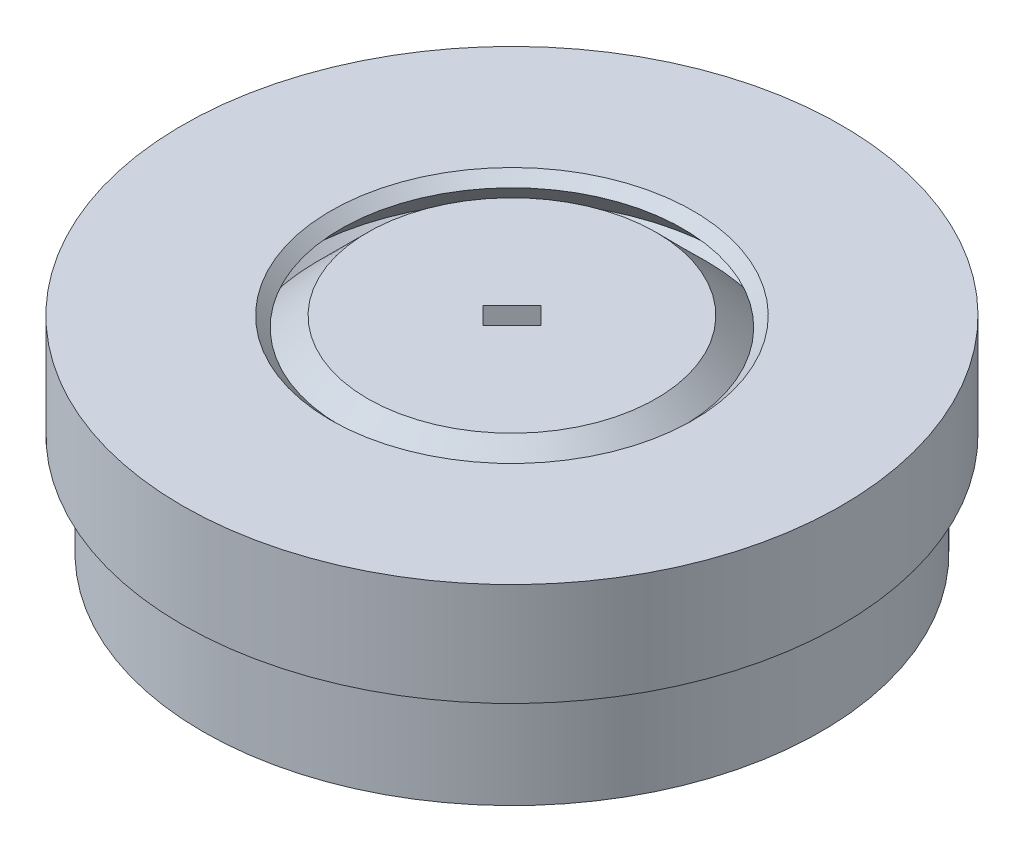
SolidWorks part; units mm, degrees
ref_plane "Front Plane" through (0, 0, 0) normal (0, 0, 1) x (1, 0, 0)
ref_plane "Top Plane" through (0, 0, 0) normal (0, 1, 0) x (1, 0, 0)
ref_plane "Right Plane" through (0, 0, 0) normal (1, 0, 0) x (0, 0, -1)
sketch "Sketch3" plane through (0, 0, 0) normal (0, 1, 0) x (1, 0, 0)
  line L0 (0, 0) -> (0, 14) construction
  line L1 (0, 11) -> (0, 14)
  line L2 (6.4656, 8.8992) -> (8.229, 11.3262)
  line L3 (10.4616, 3.3992) -> (13.3148, 4.3262)
  line L4 (10.4616, -3.3992) -> (13.3148, -4.3262)
  line L5 (6.4656, -8.8992) -> (8.229, -11.3262)
  line L6 (0, -11) -> (0, -14)
  line L7 (-6.4656, -8.8992) -> (-8.229, -11.3262)
  line L8 (-10.4616, -3.3992) -> (-13.3148, -4.3262)
  line L9 (-10.4616, 3.3992) -> (-13.3148, 4.3262)
  line L10 (-6.4656, 8.8992) -> (-8.229, 11.3262)
  line L12 (3, 3) -> (-3, 3)
  line L13 (3, 3) -> (3, -3)
  line L14 (3, -3) -> (-3, -3)
  line L15 (-3, 3) -> (-3, -3)
  line L16 (0, -3) -> (0, 3) construction
  line L17 (3, 0) -> (-3, 0) construction
  circle A0 centre (0, 0) radius 15
  circle A1 centre (0, 0) radius 14 construction
  spline S0 degree 4 poles (-0.6778, 10.6763) (-0.6286, 10.7014) (-0.5336, 10.7495) (-0.4182, 10.8106) (-0.084, 10.9641) (0.0577, 11.0264) (0.4379, 11.1818) (0.6637, 11.2619) (0.971, 11.3685) (1.234, 11.4472) (1.5272, 11.5305) (1.8056, 11.5989) (2.0959, 11.6642) (2.3817, 11.7192) (2.6725, 11.7684) (2.9623, 11.8092) (3.2542, 11.8431) (3.5945, 11.8737) (4.009, 11.8986) (4.4979, 11.9088) (4.9859, 11.897) (5.4262, 11.8684) (5.7898, 11.8338) (6.0839, 11.7981) (6.4416, 11.7478) (6.8131, 11.6815) (7.1561, 11.6125) (7.5364, 11.5205) (7.7792, 11.459) (8.1801, 11.3427) (8.3369, 11.2932) (8.7269, 11.165) (8.8594, 11.1137) (8.9726, 11.0725) (9.0307, 11.0511) knots 0 0 0 0 0 0.018755 0.037509 0.074516 0.103872 0.133229 0.162585 0.191942 0.221299 0.250655 0.280012 0.309368 0.338725 0.368082 0.397438 0.426795 0.456151 0.504872 0.563586 0.622299 0.651656 0.681012 0.710369 0.739725 0.798439 0.827795 0.857152 0.886508 0.915865 0.957933 0.978966 1 1 1 1 1 construction
  spline S1 degree 4 poles (0, 11) (0.0566, 11.0246) (0.1702, 11.0724) (0.4379, 11.1818) (0.6637, 11.2619) (0.971, 11.3685) (1.234, 11.4472) (1.5272, 11.5305) (1.8056, 11.5989) (2.0959, 11.6642) (2.3817, 11.7192) (2.6725, 11.7684) (2.9623, 11.8092) (3.2542, 11.8431) (3.5945, 11.8737) (4.009, 11.8986) (4.4979, 11.9088) (4.9859, 11.897) (5.4262, 11.8684) (5.7898, 11.8338) (6.0839, 11.7981) (6.4416, 11.7478) (6.8131, 11.6815) (7.1561, 11.6125) (7.5364, 11.5205) (7.7792, 11.459) (8.0505, 11.3803) (8.17, 11.3445) (8.229, 11.3262) knots 0.074516 0.074516 0.074516 0.074516 0.074516 0.103872 0.133229 0.162585 0.191942 0.221299 0.250655 0.280012 0.309368 0.338725 0.368082 0.397438 0.426795 0.456151 0.504872 0.563586 0.622299 0.651656 0.681012 0.710369 0.739725 0.798439 0.827795 0.857152 0.886508 0.915865 0.915865 0.915865 0.915865 0.915865
  spline S2 degree 4 poles (5.727, 9.0357) (5.7816, 9.0271) (5.8867, 9.0101) (6.016, 8.9918) (6.3766, 8.9195) (6.5279, 8.8866) (6.9268, 8.7889) (7.1565, 8.7209) (7.4678, 8.6266) (7.7268, 8.5357) (8.013, 8.4307) (8.2785, 8.3224) (8.5517, 8.2045) (8.8152, 8.0811) (9.0794, 7.95) (9.3378, 7.8126) (9.5939, 7.6685) (9.8872, 7.4932) (10.2371, 7.2697) (10.6387, 6.9906) (11.0265, 6.6943) (11.3659, 6.4123) (11.6398, 6.1706) (11.8567, 5.9689) (12.1165, 5.7179) (12.3781, 5.4459) (12.6151, 5.1885) (12.8687, 4.8905) (13.029, 4.698) (13.2848, 4.3683) (13.3827, 4.236) (13.6228, 3.9031) (13.6999, 3.7838) (13.7672, 3.6839) (13.8017, 3.6324) knots 0 0 0 0 0 0.018755 0.037509 0.074516 0.103872 0.133229 0.162585 0.191942 0.221299 0.250655 0.280012 0.309368 0.338725 0.368082 0.397438 0.426795 0.456151 0.504872 0.563586 0.622299 0.651656 0.681012 0.710369 0.739725 0.798439 0.827795 0.857152 0.886508 0.915865 0.957933 0.978966 1 1 1 1 1 construction
  spline S3 degree 4 poles (6.4656, 8.8992) (6.5259, 8.8858) (6.6459, 8.8577) (6.9268, 8.7889) (7.1565, 8.7209) (7.4678, 8.6266) (7.7268, 8.5357) (8.013, 8.4307) (8.2785, 8.3224) (8.5517, 8.2045) (8.8152, 8.0811) (9.0794, 7.95) (9.3378, 7.8126) (9.5939, 7.6685) (9.8872, 7.4932) (10.2371, 7.2697) (10.6387, 6.9906) (11.0265, 6.6943) (11.3659, 6.4123) (11.6398, 6.1706) (11.8567, 5.9689) (12.1165, 5.7179) (12.3781, 5.4459) (12.6151, 5.1885) (12.8687, 4.8905) (13.029, 4.698) (13.2021, 4.4749) (13.2778, 4.3756) (13.3148, 4.3262) knots 0.074516 0.074516 0.074516 0.074516 0.074516 0.103872 0.133229 0.162585 0.191942 0.221299 0.250655 0.280012 0.309368 0.338725 0.368082 0.397438 0.426795 0.456151 0.504872 0.563586 0.622299 0.651656 0.681012 0.710369 0.739725 0.798439 0.827795 0.857152 0.886508 0.915865 0.915865 0.915865 0.915865 0.915865
  spline S4 degree 4 poles (9.9443, 3.9438) (9.9834, 3.9047) (10.0585, 3.8292) (10.1522, 3.7384) (10.4015, 3.468) (10.5046, 3.3524) (10.7698, 3.0389) (10.9158, 2.8489) (11.1122, 2.5895) (11.2683, 2.3638) (11.4381, 2.1106) (11.5892, 1.867) (11.7409, 1.6111) (11.8816, 1.3563) (12.0183, 1.095) (12.1466, 0.8319) (12.2691, 0.5648) (12.4033, 0.2506) (12.5551, -0.1359) (12.7158, -0.5977) (12.8555, -1.0654) (12.9643, -1.493) (13.0438, -1.8496) (13.1007, -2.1403) (13.1634, -2.496) (13.2151, -2.8698) (13.2555, -3.2174) (13.2855, -3.6076) (13.3021, -3.8575) (13.3153, -4.2746) (13.3167, -4.4391) (13.3153, -4.8496) (13.3075, -4.9915) (13.3032, -5.1118) (13.3009, -5.1737) knots 0 0 0 0 0 0.018755 0.037509 0.074516 0.103872 0.133229 0.162585 0.191942 0.221299 0.250655 0.280012 0.309368 0.338725 0.368082 0.397438 0.426795 0.456151 0.504872 0.563586 0.622299 0.651656 0.681012 0.710369 0.739725 0.798439 0.827795 0.857152 0.886508 0.915865 0.957933 0.978966 1 1 1 1 1 construction
  spline S5 degree 4 poles (10.4616, 3.3992) (10.5025, 3.3529) (10.583, 3.2597) (10.7698, 3.0389) (10.9158, 2.8489) (11.1122, 2.5895) (11.2683, 2.3638) (11.4381, 2.1106) (11.5892, 1.867) (11.7409, 1.6111) (11.8816, 1.3563) (12.0183, 1.095) (12.1466, 0.8319) (12.2691, 0.5648) (12.4033, 0.2506) (12.5551, -0.1359) (12.7158, -0.5977) (12.8555, -1.0654) (12.9643, -1.493) (13.0438, -1.8496) (13.1007, -2.1403) (13.1634, -2.496) (13.2151, -2.8698) (13.2555, -3.2174) (13.2855, -3.6076) (13.3021, -3.8575) (13.311, -4.1398) (13.3139, -4.2645) (13.3148, -4.3262) knots 0.074516 0.074516 0.074516 0.074516 0.074516 0.103872 0.133229 0.162585 0.191942 0.221299 0.250655 0.280012 0.309368 0.338725 0.368082 0.397438 0.426795 0.456151 0.504872 0.563586 0.622299 0.651656 0.681012 0.710369 0.739725 0.798439 0.827795 0.857152 0.886508 0.915865 0.915865 0.915865 0.915865 0.915865
  spline S6 degree 4 poles (10.3632, -2.6545) (10.3719, -2.7091) (10.3882, -2.8143) (10.4107, -2.9429) (10.4535, -3.3082) (10.4689, -3.4622) (10.4992, -3.8718) (10.5056, -4.1113) (10.512, -4.4366) (10.5056, -4.711) (10.4942, -5.0156) (10.4732, -5.3015) (10.4456, -5.5978) (10.4097, -5.8866) (10.3666, -6.1783) (10.3158, -6.4665) (10.2579, -6.7546) (10.1818, -7.0878) (10.0774, -7.4896) (9.936, -7.9578) (9.774, -8.4182) (9.6108, -8.8281) (9.4655, -9.1633) (9.3407, -9.4319) (9.1823, -9.7566) (9.0044, -10.0894) (8.8328, -10.3943) (8.6277, -10.7276) (8.4943, -10.9395) (8.2597, -11.2848) (8.1642, -11.4187) (7.9218, -11.7499) (7.8321, -11.8601) (7.7579, -11.955) (7.7196, -12.0037) knots 0 0 0 0 0 0.018755 0.037509 0.074516 0.103872 0.133229 0.162585 0.191942 0.221299 0.250655 0.280012 0.309368 0.338725 0.368082 0.397438 0.426795 0.456151 0.504872 0.563586 0.622299 0.651656 0.681012 0.710369 0.739725 0.798439 0.827795 0.857152 0.886508 0.915865 0.957933 0.978966 1 1 1 1 1 construction
  spline S7 degree 4 poles (10.4616, -3.3992) (10.4675, -3.4606) (10.4779, -3.5834) (10.4992, -3.8718) (10.5056, -4.1113) (10.512, -4.4366) (10.5056, -4.711) (10.4942, -5.0156) (10.4732, -5.3015) (10.4456, -5.5978) (10.4097, -5.8866) (10.3666, -6.1783) (10.3158, -6.4665) (10.2579, -6.7546) (10.1818, -7.0878) (10.0774, -7.4896) (9.936, -7.9578) (9.774, -8.4182) (9.6108, -8.8281) (9.4655, -9.1633) (9.3407, -9.4319) (9.1823, -9.7566) (9.0044, -10.0894) (8.8328, -10.3943) (8.6277, -10.7276) (8.4943, -10.9395) (8.3355, -11.1732) (8.2645, -11.2758) (8.229, -11.3262) knots 0.074516 0.074516 0.074516 0.074516 0.074516 0.103872 0.133229 0.162585 0.191942 0.221299 0.250655 0.280012 0.309368 0.338725 0.368082 0.397438 0.426795 0.456151 0.504872 0.563586 0.622299 0.651656 0.681012 0.710369 0.739725 0.798439 0.827795 0.857152 0.886508 0.915865 0.915865 0.915865 0.915865 0.915865
  spline S8 degree 4 poles (6.8238, -8.2389) (6.7987, -8.2881) (6.75, -8.3829) (6.6926, -8.5001) (6.5125, -8.8208) (6.4344, -8.9545) (6.2182, -9.3037) (6.0826, -9.5012) (5.8967, -9.7681) (5.7302, -9.9863) (5.5419, -10.2261) (5.3569, -10.445) (5.1604, -10.6685) (4.9615, -10.881) (4.7552, -11.0917) (4.5447, -11.295) (4.3285, -11.4941) (4.0712, -11.7188) (3.7505, -11.9826) (3.3609, -12.2782) (2.9593, -12.5555) (2.5862, -12.7912) (2.2717, -12.9769) (2.0128, -13.1209) (1.6938, -13.2904) (1.3544, -13.4552) (1.0362, -13.601) (0.6745, -13.7501) (0.4419, -13.8431) (0.0492, -13.9845) (-0.1068, -14.0367) (-0.4976, -14.1622) (-0.6349, -14.1986) (-0.7507, -14.2318) (-0.8103, -14.2487) knots 0 0 0 0 0 0.018755 0.037509 0.074516 0.103872 0.133229 0.162585 0.191942 0.221299 0.250655 0.280012 0.309368 0.338725 0.368082 0.397438 0.426795 0.456151 0.504872 0.563586 0.622299 0.651656 0.681012 0.710369 0.739725 0.798439 0.827795 0.857152 0.886508 0.915865 0.957933 0.978966 1 1 1 1 1 construction
  spline S9 degree 4 poles (6.4656, -8.8992) (6.4343, -8.9523) (6.3705, -9.0578) (6.2182, -9.3037) (6.0826, -9.5012) (5.8967, -9.7681) (5.7302, -9.9863) (5.5419, -10.2261) (5.3569, -10.445) (5.1604, -10.6685) (4.9615, -10.881) (4.7552, -11.0917) (4.5447, -11.295) (4.3285, -11.4941) (4.0712, -11.7188) (3.7505, -11.9826) (3.3609, -12.2782) (2.9593, -12.5555) (2.5862, -12.7912) (2.2717, -12.9769) (2.0128, -13.1209) (1.6938, -13.2904) (1.3544, -13.4552) (1.0362, -13.601) (0.6745, -13.7501) (0.4419, -13.8431) (0.1762, -13.9388) (0.0584, -13.9801) (0, -14) knots 0.074516 0.074516 0.074516 0.074516 0.074516 0.103872 0.133229 0.162585 0.191942 0.221299 0.250655 0.280012 0.309368 0.338725 0.368082 0.397438 0.426795 0.456151 0.504872 0.563586 0.622299 0.651656 0.681012 0.710369 0.739725 0.798439 0.827795 0.857152 0.886508 0.915865 0.915865 0.915865 0.915865 0.915865
  spline S10 degree 4 poles (0.6778, -10.6763) (0.6286, -10.7014) (0.5336, -10.7495) (0.4182, -10.8106) (0.084, -10.9641) (-0.0577, -11.0264) (-0.4379, -11.1818) (-0.6637, -11.2619) (-0.971, -11.3685) (-1.234, -11.4472) (-1.5272, -11.5305) (-1.8056, -11.5989) (-2.0959, -11.6642) (-2.3817, -11.7192) (-2.6725, -11.7684) (-2.9623, -11.8092) (-3.2542, -11.8431) (-3.5945, -11.8737) (-4.009, -11.8986) (-4.4979, -11.9088) (-4.9859, -11.897) (-5.4262, -11.8684) (-5.7898, -11.8338) (-6.0839, -11.7981) (-6.4416, -11.7478) (-6.8131, -11.6815) (-7.1561, -11.6125) (-7.5364, -11.5205) (-7.7792, -11.459) (-8.1801, -11.3427) (-8.3369, -11.2932) (-8.7269, -11.165) (-8.8594, -11.1137) (-8.9726, -11.0725) (-9.0307, -11.0511) knots 0 0 0 0 0 0.018755 0.037509 0.074516 0.103872 0.133229 0.162585 0.191942 0.221299 0.250655 0.280012 0.309368 0.338725 0.368082 0.397438 0.426795 0.456151 0.504872 0.563586 0.622299 0.651656 0.681012 0.710369 0.739725 0.798439 0.827795 0.857152 0.886508 0.915865 0.957933 0.978966 1 1 1 1 1 construction
  spline S11 degree 4 poles (0, -11) (-0.0566, -11.0246) (-0.1702, -11.0724) (-0.4379, -11.1818) (-0.6637, -11.2619) (-0.971, -11.3685) (-1.234, -11.4472) (-1.5272, -11.5305) (-1.8056, -11.5989) (-2.0959, -11.6642) (-2.3817, -11.7192) (-2.6725, -11.7684) (-2.9623, -11.8092) (-3.2542, -11.8431) (-3.5945, -11.8737) (-4.009, -11.8986) (-4.4979, -11.9088) (-4.9859, -11.897) (-5.4262, -11.8684) (-5.7898, -11.8338) (-6.0839, -11.7981) (-6.4416, -11.7478) (-6.8131, -11.6815) (-7.1561, -11.6125) (-7.5364, -11.5205) (-7.7792, -11.459) (-8.0505, -11.3803) (-8.17, -11.3445) (-8.229, -11.3262) knots 0.074516 0.074516 0.074516 0.074516 0.074516 0.103872 0.133229 0.162585 0.191942 0.221299 0.250655 0.280012 0.309368 0.338725 0.368082 0.397438 0.426795 0.456151 0.504872 0.563586 0.622299 0.651656 0.681012 0.710369 0.739725 0.798439 0.827795 0.857152 0.886508 0.915865 0.915865 0.915865 0.915865 0.915865
  spline S12 degree 4 poles (-5.727, -9.0357) (-5.7816, -9.0271) (-5.8867, -9.0101) (-6.016, -8.9918) (-6.3766, -8.9195) (-6.5279, -8.8866) (-6.9268, -8.7889) (-7.1565, -8.7209) (-7.4678, -8.6266) (-7.7268, -8.5357) (-8.013, -8.4307) (-8.2785, -8.3224) (-8.5517, -8.2045) (-8.8152, -8.0811) (-9.0794, -7.95) (-9.3378, -7.8126) (-9.5939, -7.6685) (-9.8872, -7.4932) (-10.2371, -7.2697) (-10.6387, -6.9906) (-11.0265, -6.6943) (-11.3659, -6.4123) (-11.6398, -6.1706) (-11.8567, -5.9689) (-12.1165, -5.7179) (-12.3781, -5.4459) (-12.6151, -5.1885) (-12.8687, -4.8905) (-13.029, -4.698) (-13.2848, -4.3683) (-13.3827, -4.236) (-13.6228, -3.9031) (-13.6999, -3.7838) (-13.7672, -3.6839) (-13.8017, -3.6324) knots 0 0 0 0 0 0.018755 0.037509 0.074516 0.103872 0.133229 0.162585 0.191942 0.221299 0.250655 0.280012 0.309368 0.338725 0.368082 0.397438 0.426795 0.456151 0.504872 0.563586 0.622299 0.651656 0.681012 0.710369 0.739725 0.798439 0.827795 0.857152 0.886508 0.915865 0.957933 0.978966 1 1 1 1 1 construction
  spline S13 degree 4 poles (-6.4656, -8.8992) (-6.5259, -8.8858) (-6.6459, -8.8577) (-6.9268, -8.7889) (-7.1565, -8.7209) (-7.4678, -8.6266) (-7.7268, -8.5357) (-8.013, -8.4307) (-8.2785, -8.3224) (-8.5517, -8.2045) (-8.8152, -8.0811) (-9.0794, -7.95) (-9.3378, -7.8126) (-9.5939, -7.6685) (-9.8872, -7.4932) (-10.2371, -7.2697) (-10.6387, -6.9906) (-11.0265, -6.6943) (-11.3659, -6.4123) (-11.6398, -6.1706) (-11.8567, -5.9689) (-12.1165, -5.7179) (-12.3781, -5.4459) (-12.6151, -5.1885) (-12.8687, -4.8905) (-13.029, -4.698) (-13.2021, -4.4749) (-13.2778, -4.3756) (-13.3148, -4.3262) knots 0.074516 0.074516 0.074516 0.074516 0.074516 0.103872 0.133229 0.162585 0.191942 0.221299 0.250655 0.280012 0.309368 0.338725 0.368082 0.397438 0.426795 0.456151 0.504872 0.563586 0.622299 0.651656 0.681012 0.710369 0.739725 0.798439 0.827795 0.857152 0.886508 0.915865 0.915865 0.915865 0.915865 0.915865
  spline S14 degree 4 poles (-9.9443, -3.9438) (-9.9834, -3.9047) (-10.0585, -3.8292) (-10.1522, -3.7384) (-10.4015, -3.468) (-10.5046, -3.3524) (-10.7698, -3.0389) (-10.9158, -2.8489) (-11.1122, -2.5895) (-11.2683, -2.3638) (-11.4381, -2.1106) (-11.5892, -1.867) (-11.7409, -1.6111) (-11.8816, -1.3563) (-12.0183, -1.095) (-12.1466, -0.8319) (-12.2691, -0.5648) (-12.4033, -0.2506) (-12.5551, 0.1359) (-12.7158, 0.5977) (-12.8555, 1.0654) (-12.9643, 1.493) (-13.0438, 1.8496) (-13.1007, 2.1403) (-13.1634, 2.496) (-13.2151, 2.8698) (-13.2555, 3.2174) (-13.2855, 3.6076) (-13.3021, 3.8575) (-13.3153, 4.2746) (-13.3167, 4.4391) (-13.3153, 4.8496) (-13.3075, 4.9915) (-13.3032, 5.1118) (-13.3009, 5.1737) knots 0 0 0 0 0 0.018755 0.037509 0.074516 0.103872 0.133229 0.162585 0.191942 0.221299 0.250655 0.280012 0.309368 0.338725 0.368082 0.397438 0.426795 0.456151 0.504872 0.563586 0.622299 0.651656 0.681012 0.710369 0.739725 0.798439 0.827795 0.857152 0.886508 0.915865 0.957933 0.978966 1 1 1 1 1 construction
  spline S15 degree 4 poles (-10.4616, -3.3992) (-10.5025, -3.3529) (-10.583, -3.2597) (-10.7698, -3.0389) (-10.9158, -2.8489) (-11.1122, -2.5895) (-11.2683, -2.3638) (-11.4381, -2.1106) (-11.5892, -1.867) (-11.7409, -1.6111) (-11.8816, -1.3563) (-12.0183, -1.095) (-12.1466, -0.8319) (-12.2691, -0.5648) (-12.4033, -0.2506) (-12.5551, 0.1359) (-12.7158, 0.5977) (-12.8555, 1.0654) (-12.9643, 1.493) (-13.0438, 1.8496) (-13.1007, 2.1403) (-13.1634, 2.496) (-13.2151, 2.8698) (-13.2555, 3.2174) (-13.2855, 3.6076) (-13.3021, 3.8575) (-13.311, 4.1398) (-13.3139, 4.2645) (-13.3148, 4.3262) knots 0.074516 0.074516 0.074516 0.074516 0.074516 0.103872 0.133229 0.162585 0.191942 0.221299 0.250655 0.280012 0.309368 0.338725 0.368082 0.397438 0.426795 0.456151 0.504872 0.563586 0.622299 0.651656 0.681012 0.710369 0.739725 0.798439 0.827795 0.857152 0.886508 0.915865 0.915865 0.915865 0.915865 0.915865
  spline S16 degree 4 poles (-10.3632, 2.6545) (-10.3719, 2.7091) (-10.3882, 2.8143) (-10.4107, 2.9429) (-10.4535, 3.3082) (-10.4689, 3.4622) (-10.4992, 3.8718) (-10.5056, 4.1113) (-10.512, 4.4366) (-10.5056, 4.711) (-10.4942, 5.0156) (-10.4732, 5.3015) (-10.4456, 5.5978) (-10.4097, 5.8866) (-10.3666, 6.1783) (-10.3158, 6.4665) (-10.2579, 6.7546) (-10.1818, 7.0878) (-10.0774, 7.4896) (-9.936, 7.9578) (-9.774, 8.4182) (-9.6108, 8.8281) (-9.4655, 9.1633) (-9.3407, 9.4319) (-9.1823, 9.7566) (-9.0044, 10.0894) (-8.8328, 10.3943) (-8.6277, 10.7276) (-8.4943, 10.9395) (-8.2597, 11.2848) (-8.1642, 11.4187) (-7.9218, 11.7499) (-7.8321, 11.8601) (-7.7579, 11.955) (-7.7196, 12.0037) knots 0 0 0 0 0 0.018755 0.037509 0.074516 0.103872 0.133229 0.162585 0.191942 0.221299 0.250655 0.280012 0.309368 0.338725 0.368082 0.397438 0.426795 0.456151 0.504872 0.563586 0.622299 0.651656 0.681012 0.710369 0.739725 0.798439 0.827795 0.857152 0.886508 0.915865 0.957933 0.978966 1 1 1 1 1 construction
  spline S17 degree 4 poles (-10.4616, 3.3992) (-10.4675, 3.4606) (-10.4779, 3.5834) (-10.4992, 3.8718) (-10.5056, 4.1113) (-10.512, 4.4366) (-10.5056, 4.711) (-10.4942, 5.0156) (-10.4732, 5.3015) (-10.4456, 5.5978) (-10.4097, 5.8866) (-10.3666, 6.1783) (-10.3158, 6.4665) (-10.2579, 6.7546) (-10.1818, 7.0878) (-10.0774, 7.4896) (-9.936, 7.9578) (-9.774, 8.4182) (-9.6108, 8.8281) (-9.4655, 9.1633) (-9.3407, 9.4319) (-9.1823, 9.7566) (-9.0044, 10.0894) (-8.8328, 10.3943) (-8.6277, 10.7276) (-8.4943, 10.9395) (-8.3355, 11.1732) (-8.2645, 11.2758) (-8.229, 11.3262) knots 0.074516 0.074516 0.074516 0.074516 0.074516 0.103872 0.133229 0.162585 0.191942 0.221299 0.250655 0.280012 0.309368 0.338725 0.368082 0.397438 0.426795 0.456151 0.504872 0.563586 0.622299 0.651656 0.681012 0.710369 0.739725 0.798439 0.827795 0.857152 0.886508 0.915865 0.915865 0.915865 0.915865 0.915865
  spline S18 degree 4 poles (-6.8238, 8.2389) (-6.7987, 8.2881) (-6.75, 8.3829) (-6.6926, 8.5001) (-6.5125, 8.8208) (-6.4344, 8.9545) (-6.2182, 9.3037) (-6.0826, 9.5012) (-5.8967, 9.7681) (-5.7302, 9.9863) (-5.5419, 10.2261) (-5.3569, 10.445) (-5.1604, 10.6685) (-4.9615, 10.881) (-4.7552, 11.0917) (-4.5447, 11.295) (-4.3285, 11.4941) (-4.0712, 11.7188) (-3.7505, 11.9826) (-3.3609, 12.2782) (-2.9593, 12.5555) (-2.5862, 12.7912) (-2.2717, 12.9769) (-2.0128, 13.1209) (-1.6938, 13.2904) (-1.3544, 13.4552) (-1.0362, 13.601) (-0.6745, 13.7501) (-0.4419, 13.8431) (-0.0492, 13.9845) (0.1068, 14.0367) (0.4976, 14.1622) (0.6349, 14.1986) (0.7507, 14.2318) (0.8103, 14.2487) knots 0 0 0 0 0 0.018755 0.037509 0.074516 0.103872 0.133229 0.162585 0.191942 0.221299 0.250655 0.280012 0.309368 0.338725 0.368082 0.397438 0.426795 0.456151 0.504872 0.563586 0.622299 0.651656 0.681012 0.710369 0.739725 0.798439 0.827795 0.857152 0.886508 0.915865 0.957933 0.978966 1 1 1 1 1 construction
  spline S19 degree 4 poles (-6.4656, 8.8992) (-6.4343, 8.9523) (-6.3705, 9.0578) (-6.2182, 9.3037) (-6.0826, 9.5012) (-5.8967, 9.7681) (-5.7302, 9.9863) (-5.5419, 10.2261) (-5.3569, 10.445) (-5.1604, 10.6685) (-4.9615, 10.881) (-4.7552, 11.0917) (-4.5447, 11.295) (-4.3285, 11.4941) (-4.0712, 11.7188) (-3.7505, 11.9826) (-3.3609, 12.2782) (-2.9593, 12.5555) (-2.5862, 12.7912) (-2.2717, 12.9769) (-2.0128, 13.1209) (-1.6938, 13.2904) (-1.3544, 13.4552) (-1.0362, 13.601) (-0.6745, 13.7501) (-0.4419, 13.8431) (-0.1762, 13.9388) (-0.0584, 13.9801) (0, 14) knots 0.074516 0.074516 0.074516 0.074516 0.074516 0.103872 0.133229 0.162585 0.191942 0.221299 0.250655 0.280012 0.309368 0.338725 0.368082 0.397438 0.426795 0.456151 0.504872 0.563586 0.622299 0.651656 0.681012 0.710369 0.739725 0.798439 0.827795 0.857152 0.886508 0.915865 0.915865 0.915865 0.915865 0.915865
  point P57 (0, 0)
  dimension "D1" = 30
  dimension "D2" = 28
  dimension "D3" = 10
  dimension "D4" = 6
  dimension "D5" = 6
extrude "Boss-Extrude1" add sketch "Sketch3" along normal blind 3 contours A0 L10 S19 L1 S1 L2 S3 L3 S5 L4 S7 L5 S9 L6 S11 L7 S13 L8 S15 L9 S17 | L13 L12 L15 L14
sketch "Sketch5" plane through (0, 0, 0) normal (1, 0, 0) x (0, 0, -1)
  line L0 (-3, 0) -> (-3, 3) construction
  line L1 (-3, 3) -> (3, 3) construction
  line L2 (3, 3) -> (3, 0) construction
  line L3 (3, 0) -> (-3, 0) construction
  line L4 (-3, 3) -> (3, 0) construction
  line L5 (-3, 0) -> (3, 3) construction
  line L6 (15, 0) -> (15, 3) construction
  line L7 (-15, 3) -> (15, 3) construction
  line L8 (-15, 3) -> (-15, 10) construction
  line L9 (-15, 10) -> (15, 10) construction
  line L10 (15, 3) -> (15, 10) construction
  line L11 (0, 10) -> (0, 3) construction
  line L12 (-15, 6.5) -> (15, 6.5) construction
  line L13 (15, 5) -> (16, 5) construction
  line L14 (-15, 10) -> (-16, 10) construction
  line L15 (-15, 10) -> (-15, 5) construction
  line L16 (-15, 5) -> (-16, 5) construction
  line L17 (-16, 10) -> (-16, 5) construction
  line L18 (-15.5, 5) -> (-15.5, 10) construction
  line L19 (-15, 7.5) -> (-16, 7.5) construction
  line L20 (15, 10) -> (16, 10) construction
  line L21 (16, 10) -> (16, 5) construction
  line L22 (-7, 10) -> (-9.5, 7.5)
  line L23 (7, 3) -> (-7, 3) construction
  line L24 (7, 3) -> (7, 10) construction
  line L25 (7, 10) -> (-7, 10) construction
  line L26 (-7, 3) -> (-7, 10) construction
  line L27 (0, 10) -> (0, 3) construction
  line L28 (7, 6.5) -> (-7, 6.5) construction
  line L29 (-7, 10) -> (7, 10) construction
  line L30 (-7, 10) -> (-7, 5) construction
  line L31 (-7, 5) -> (7, 5) construction
  line L32 (7, 10) -> (7, 5) construction
  line L33 (0, 5) -> (0, 10) construction
  line L34 (-7, 7.5) -> (7, 7.5) construction
  line L35 (7.8, 5) -> (-7.8, 5) construction
  line L36 (7.8, 5) -> (7.8, 10) construction
  line L37 (7.8, 10) -> (-7.8, 10) construction
  line L38 (-7.8, 5) -> (-7.8, 10) construction
  line L39 (0, 10) -> (0, 5) construction
  line L40 (7.8, 7.5) -> (-7.8, 7.5) construction
  line L41 (-9.5, 7.5) -> (-7, 5)
  line L42 (-7.8, 10) -> (-10.3, 7.5)
  line L43 (-10.3, 7.5) -> (-7.8, 5)
  line L44 (-7, 10) -> (0, 10)
  line L45 (0, 10) -> (0, 3)
  line L48 (-7, 5) -> (-7, 3)
  line L52 (-7.8, 5) -> (-10.3, 5)
  line L53 (-10.3, 5) -> (-10.3, 3)
  line L54 (-10.3, 3) -> (-15, 3)
  line L55 (-15, 3) -> (-15, 5)
  line L56 (-15, 5) -> (-16, 5)
  line L57 (-16, 5) -> (-16, 10)
  line L58 (-16, 10) -> (-7.8, 10)
  line L59 (0, 3) -> (-7, 3)
  point P20 (0, 6.5)
  point P27 (0, 7.5)
  point P289 (-15.5, 7.5)
  point P440 (0, 6.5)
  point P493 (0, 7.5)
  dimension "D1" = 7
  dimension "D2" = 5
  dimension "D3" = 1
  dimension "D4" = 14
  dimension "D5" = 5
  dimension "D6" = 0.8
  dimension "D7" = 90
  dimension "D8" = 90
  dimension "D9" = 2.5
revolve "Revolve1" add sketch "Sketch5" angle 360 about L45
fillet "Fillet2" radius 0.5 1 edges at (0, 3, 10.3)
fillet "Fillet3" radius 0.5 1 edges at (0, 3, 7)
chamfer "Chamfer1" distance 0.5 angle 45 4 edges at (3, 0, 0) (0, 0, -3) (-3, 0, 0) (0, 0, 3)
chamfer "Chamfer2" distance 1 angle 45 1 edges at (0, 10, 7.8)
sketch "Sketch6" plane through (0, 0, 0) normal (0, -1, 0) x (1, 0, 0)
  line L0 (2.5, -2.5) -> (-2.5, 2.5) construction
  line L1 (-0.2828, 1.1314) -> (1.1314, -0.2828)
  line L2 (-0.2828, 1.1314) -> (-1.1314, 0.2828)
  line L3 (1.1314, -0.2828) -> (0.2828, -1.1314)
  line L4 (-1.1314, 0.2828) -> (0.2828, -1.1314)
  line L5 (-0.2828, 1.1314) -> (0.2828, -1.1314) construction
  line L6 (1.1314, -0.2828) -> (-1.1314, 0.2828) construction
  point P5 (0, 0)
  dimension "D1" = 1.2
  dimension "D2" = 2
extrude "Cut-Extrude1" cut sketch "Sketch6" against normal through all
